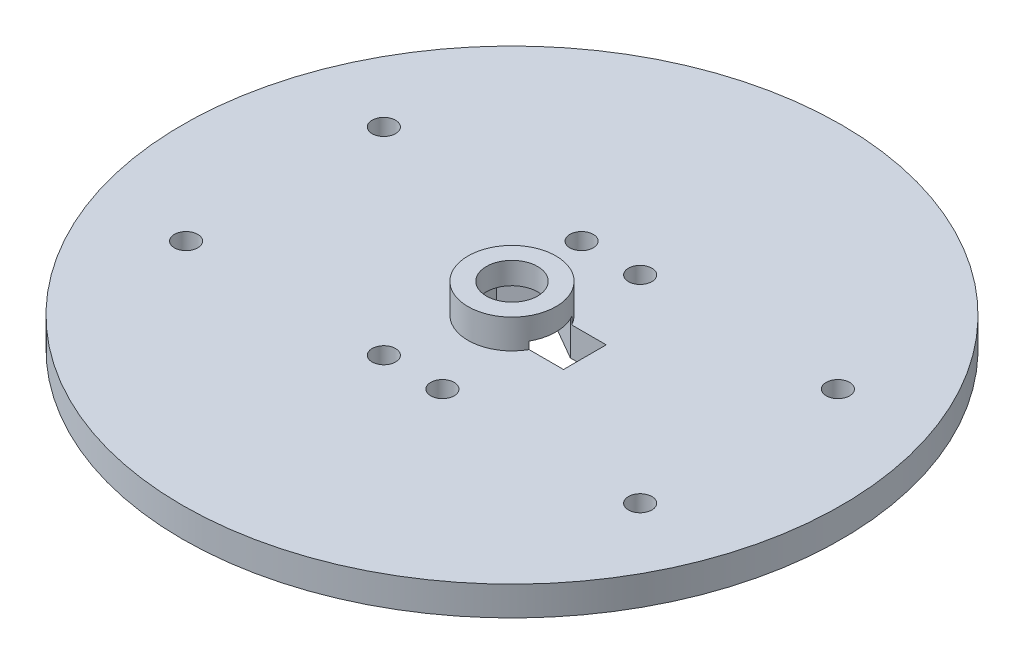
SolidWorks part; units mm, degrees
material "PET"
ref_plane "Спереди" through (0, 0, 0) normal (0, 0, 1) x (1, 0, 0)
ref_plane "Сверху" through (0, 0, 0) normal (0, 1, 0) x (1, 0, 0)
ref_plane "Справа" through (0, 0, 0) normal (1, 0, 0) x (0, 0, -1)
sketch "Эскиз1" plane through (0, 0, 0) normal (0, 1, 0) x (1, 0, 0)
  circle A0 centre (0, 0) radius 45
  dimension "D1" = 90
extrude "Бобышка-Вытянуть1" add sketch "Эскиз1" along normal blind 4
sketch "Эскиз13" plane through (0, 4, 0) normal (0, 1, 0) x (1, 0, 0)
  circle A0 centre (0, 0) radius 6
  dimension "D1" = 12
extrude "Бобышка-Вытянуть5" add sketch "Эскиз13" along normal blind 4
sketch "Эскиз14" plane through (0, 8, 0) normal (0, 1, 0) x (1, 0, 0)
  line L0 (-1.6583, 2.5) -> (1.6583, 2.5)
  arc A0 (-1.6583, 2.5) -> (1.6583, 2.5) centre (0, 0) ccw
  dimension "D1" = 6
  dimension "D2" = 2.5
sketch "Эскиз15" plane through (0, 4, 0) normal (0, 1, 0) x (1, 0, 0)
  line L0 (0, 0) -> (0, 46.3584) construction
  line L1 (0, 0) -> (57.0792, 0) construction
  circle A0 centre (-4, 13.5) radius 1.6
  circle A1 centre (-4, -13.5) radius 1.6
  circle A2 centre (4, -13.5) radius 1.6
  circle A3 centre (4, 13.5) radius 1.6
  dimension "D1" = 3.2
  dimension "D2" = 27
  dimension "D3" = 8
extrude "Вырез-Вытянуть5" cut sketch "Эскиз15" against normal through all
sketch "Эскиз19" plane through (0, 0, 0) normal (0, -1, 0) x (1, 0, 0)
  line L0 (0, 0) -> (0, -15.9132) construction
  line L1 (5.05, 2.9156) -> (0, 5.8312)
  line L2 (0, 5.8312) -> (-5.05, 2.9156)
  line L3 (-5.05, 2.9156) -> (-5.05, -2.9156)
  line L4 (-5.05, -2.9156) -> (0, -5.8312)
  line L5 (0, -5.8312) -> (5.05, -2.9156)
  line L7 (9.95, 2.9156) -> (9.95, -2.9156)
  line L8 (9.95, -2.9156) -> (5.05, -2.9156)
  line L9 (9.95, 2.9156) -> (5.05, 2.9156)
  line L11 (5.05, 0) -> (5.05, 2.9156) [skipped]
  circle A0 centre (0, 0) radius 5.05 construction
  dimension "D2" = 15
extrude "Вырез-Вытянуть6" cut sketch "Эскиз19" against normal blind 5
sketch "Эскиз20" plane through (0, 5, 0) normal (0, -1, 0) x (1, 0, 0)
  circle A0 centre (0, 0) radius 3.5
  dimension "D1" = 7
extrude "Вырез-Вытянуть7" cut sketch "Эскиз20" against normal blind 5
sketch "Эскиз21" plane through (0, 0, 0) normal (0, -1, 0) x (1, 0, 0)
  line L0 (0, 0) -> (0, -34.8146) construction
  circle A0 centre (4, 13.5) radius 1.6
  circle A1 centre (4, -13.5) radius 1.6
  circle A2 centre (31, 13.5) radius 1.6
  circle A3 centre (31, -13.5) radius 1.6
  circle A4 centre (-31, 13.5) radius 1.6
  circle A5 centre (-31, -13.5) radius 1.6
  dimension "D3" = 3.2
  dimension "D4" = 3.2
  dimension "D1" = 27
  dimension "D2" = 27
extrude "Вырез-Вытянуть8" cut sketch "Эскиз21" against normal blind 5
